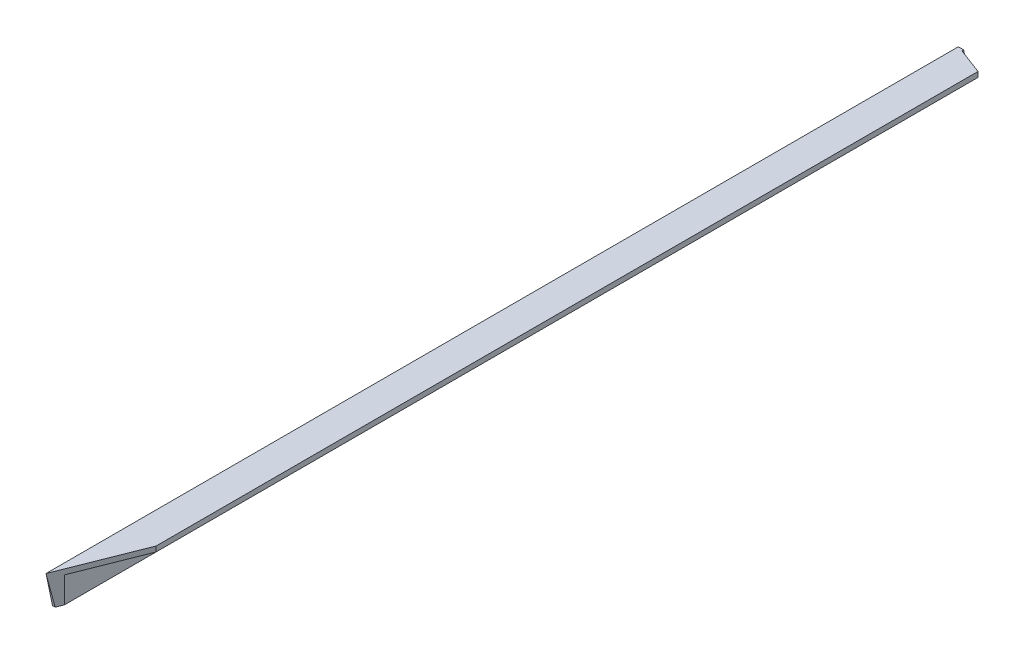
SolidWorks part; units mm, degrees
ref_plane "Front Plane" through (0, 0, 0) normal (0, 0, 1) x (1, 0, 0)
ref_plane "Top Plane" through (0, 0, 0) normal (0, 1, 0) x (1, 0, 0)
ref_plane "Right Plane" through (0, 0, 0) normal (1, 0, 0) x (0, 0, -1)
sketch "Sketch2" plane through (0, 0, 0) normal (0, 0, 1) x (1, 0, 0)
  line L0 (0, 0) -> (0, -38.1)
  line L1 (0, -38.1) -> (6.35, -38.1)
  line L2 (6.35, -38.1) -> (6.35, -6.35)
  line L3 (6.35, -6.35) -> (38.1, -6.35)
  line L4 (38.1, -6.35) -> (38.1, 0)
  line L5 (38.1, 0) -> (0, 0)
  dimension "D1" = 38.1
  dimension "D2" = 6.35
extrude "Boss-Extrude1" add sketch "Sketch2" along normal blind 1143
sketch "Sketch3" plane through (0, 0, 0) normal (0, 1, 0) x (1, 0, 0)
  line L0 (6.35, -82.7187) -> (6.35, -31.75)
  line L1 (38.1, -1143) -> (38.1, 0) construction
  line L2 (6.35, -31.75) -> (38.1, -43.791)
  line L3 (0, -1143) -> (0, 0) construction
  line L4 (38.1, -43.791) -> (38.1, -82.7187)
  line L5 (38.1, -82.7187) -> (6.35, -82.7187)
  line L6 (0, -1143) -> (38.1, -1143)
  line L7 (0, -1143) -> (38.1, -1046.7724)
  line L8 (38.1, -1046.7724) -> (38.1, -995.9724)
  line L9 (38.1, -995.9724) -> (0, -995.9724)
  line L10 (0, -995.9724) -> (0, -1143)
  line L11 (38.1, -1143) -> (38.1, -1046.7724)
  line L12 (38.1, 0) -> (0, 0) construction
  line L13 (38.1, 0) -> (38.1, -43.791)
  line L15 (6.35, 0) -> (6.35, -31.75)
  line L16 (0, 0) -> (38.1, 0)
  line L17 (38.1, 0) -> (38.1, -43.791)
  line M21 (38.1, 0) -> (0, 0)
  line M22 (0, 0) -> (0, -1143)
  line M23 (0, -1143) -> (38.1, -1143)
  line M24 (38.1, -1143) -> (38.1, 0)
  dimension "D1" = 69.231
  dimension "D2" = 21.6
  dimension "D3" = 38.1
  dimension "D4" = 50.8
  dimension "D5" = 31.75
  dimension "D6" = 31.75
extrude "Y Face" cut sketch "Sketch3" against normal through all contours L2 M22 M24 M21 | L7 M23 M24
sketch "Sketch4" plane through (0, 0, 0) normal (-1, 0, 0) x (0, 0, 1)
  line L4 (1143, 0) -> (1143, -38.1) construction
  line L5 (1143, 0) -> (0, 0) construction
  line L8 (1092.2, -38.1) -> (1092.2, 0)
  line L9 (1135.0066, -38.1) -> (1143, -38.1)
  line L10 (1092.2, 0) -> (1143, 0)
  line L11 (1143, -38.1) -> (1143, 0)
  line L12 (1143, 0) -> (1135.0066, -38.1)
  line L13 (1135.0066, -38.1) -> (1092.2, -38.1)
  line L14 (72.4722, 0) -> (72.4722, -38.1)
  line L15 (72.4722, -38.1) -> (21.6722, -38.1)
  line L16 (21.6722, -38.1) -> (29.6655, 0)
  line L17 (29.6655, 0) -> (72.4722, 0)
  line L18 (21.6722, -38.1) -> (0, -38.1) construction
  line L19 (1143, -38.1) -> (0, -38.1) construction
  point P0 (72.4722, -38.1)
  point P3 (-48.2994, -100.573)
  point P16 (0, -38.1)
  point P22 (0, 43.7769)
  dimension "D1" = 101.849
  dimension "D2" = 78.151
  dimension "D5" = 38.1
  dimension "D6" = 50.8
  dimension "D7" = 21.6722
  dimension "D8" = 38.1
  dimension "D9" = 50.8
extrude "X Face" cut sketch "Sketch4" against normal through all
